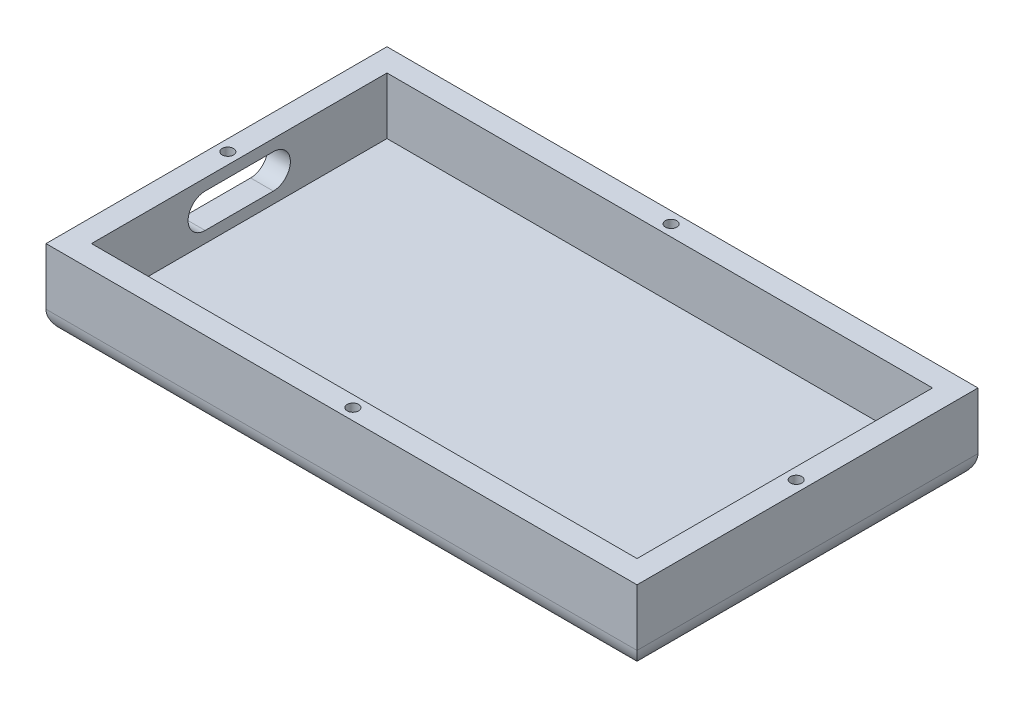
SolidWorks part; units mm, degrees
ref_plane "Front Plane" through (0, 0, 0) normal (0, 0, 1) x (1, 0, 0)
ref_plane "Top Plane" through (0, 0, 0) normal (0, 1, 0) x (1, 0, 0)
ref_plane "Right Plane" through (0, 0, 0) normal (1, 0, 0) x (0, 0, -1)
sketch "Sketch1" plane through (0, 0, 0) normal (0, 1, 0) x (1, 0, 0)
  line L1 (0, 0) -> (66.04, 0)
  line L2 (0, 0) -> (0, 38.1)
  line L3 (0, 38.1) -> (66.04, 38.1)
  line L4 (66.04, 0) -> (66.04, 38.1)
  dimension "D1" = 38.1
  dimension "D2" = 66.04
extrude "Boss-Extrude3" add sketch "Sketch1" along normal blind 17.78
sketch "Sketch3" plane through (0, 17.78, 0) normal (0, 1, 0) x (1, 0, 0)
  line L0 (0, 38.1) -> (0, 0) construction
  line L1 (2.54, 35.56) -> (63.5, 35.56)
  line L2 (2.54, 35.56) -> (2.54, 2.54)
  line L3 (2.54, 2.54) -> (63.5, 2.54)
  line L4 (63.5, 35.56) -> (63.5, 2.54)
  line L5 (66.04, 0) -> (66.04, 38.1) construction
  line L6 (66.04, 38.1) -> (0, 38.1) construction
  line L7 (0, 0) -> (66.04, 0) construction
  dimension "D1" = 2.54
  dimension "D2" = 2.54
  dimension "D3" = 2.54
  dimension "D4" = 2.54
extrude "Cut-Extrude1" cut sketch "Sketch3" against normal blind 15.24
sketch "Sketch4" plane through (66.04, 0, 0) normal (1, 0, 0) x (0, 0, -1)
  line L0 (38.1, 17.78) -> (38.1, 0) construction
  line L1 (0, 17.78) -> (38.1, 17.78)
  line L2 (0, 17.78) -> (0, 8.89)
  line L3 (0, 8.89) -> (38.1, 8.89)
  line L4 (38.1, 17.78) -> (38.1, 8.89)
  line M6 (38.1, 0) -> (38.1, 17.78)
  line M7 (38.1, 17.78) -> (0, 17.78)
  line M8 (0, 17.78) -> (0, 0)
extrude "Cut-Extrude2" cut sketch "Sketch4" against normal blind 66.04 contours L3 M8 M6 M7
sketch "Sketch5" plane through (0, 8.89, 0) normal (0, 1, 0) x (1, 0, 0)
  line L0 (0, 0) -> (0, 38.1) construction
  line L1 (63.5, 35.56) -> (2.54, 35.56) construction
  line L2 (2.54, 2.54) -> (63.5, 2.54) construction
  line L3 (2.54, 35.56) -> (2.54, 2.54) construction
  line L4 (0, 38.1) -> (66.04, 38.1) construction
  line L5 (63.5, 2.54) -> (63.5, 35.56) construction
  line L6 (0, 0) -> (66.04, 0) construction
  circle A0 centre (33.02, 36.83) radius 0.635
  circle A1 centre (33.02, 1.27) radius 0.635
  circle A2 centre (1.27, 19.05) radius 0.635
  circle A3 centre (64.77, 19.05) radius 0.635
  dimension "D3" = 1.27
  dimension "D4" = 1.27
  dimension "D7" = 1.27
  dimension "D10" = 1.27
  dimension "D1" = 33.02
  dimension "D2" = 1.27
  dimension "D5" = 1.27
  dimension "D6" = 33.02
  dimension "D8" = 1.27
  dimension "D9" = 19.05
  dimension "D11" = 1.27
  dimension "D12" = 19.05
extrude "Cut-Extrude3" cut sketch "Sketch5" against normal blind 5.08
sketch "Sketch6" plane through (0, 0, 0) normal (-1, 0, 0) x (0, 0, 1)
  line L1 (-22.86, 7.62) -> (-15.24, 7.62)
  line L3 (-22.86, 3.81) -> (-15.24, 3.81)
  line L4 (-38.1, 8.89) -> (-38.1, 0) construction
  line L5 (0, 8.89) -> (0, 0) construction
  arc A0 (-22.86, 7.62) -> (-22.86, 3.81) centre (-22.86, 5.715) ccw
  arc A1 (-15.24, 3.81) -> (-15.24, 7.62) centre (-15.24, 5.715) ccw
  point P11 (0, 0)
  dimension "D3" = 1.905
  dimension "D4" = 1.905
  dimension "D6" = 15.24
  dimension "D2" = 3.81
  dimension "D5" = 15.24
extrude "Cut-Extrude5" cut sketch "Sketch6" against normal blind 2.54
fillet "Fillet1" radius 2.54 4 edges at (33.02, 0, 0) (66.04, 0, -19.05) (33.02, 0, -38.1) (0, 0, -19.05)
sketch "Sketch7" plane through (0, 0, 0) normal (0, -1, 0) x (1, 0, 0)
  line L0 (63.5, -35.56) -> (63.5, -2.54) construction
  line L4 (2.54, -35.56) -> (63.5, -35.56) construction
  circle A0 centre (33.02, -30.48) radius 1.5875
  dimension "D1" = 3.175
  dimension "D2" = 30.48
  dimension "D3" = 5.08
extrude "Cut-Extrude6" cut sketch "Sketch7" against normal blind 1.27
